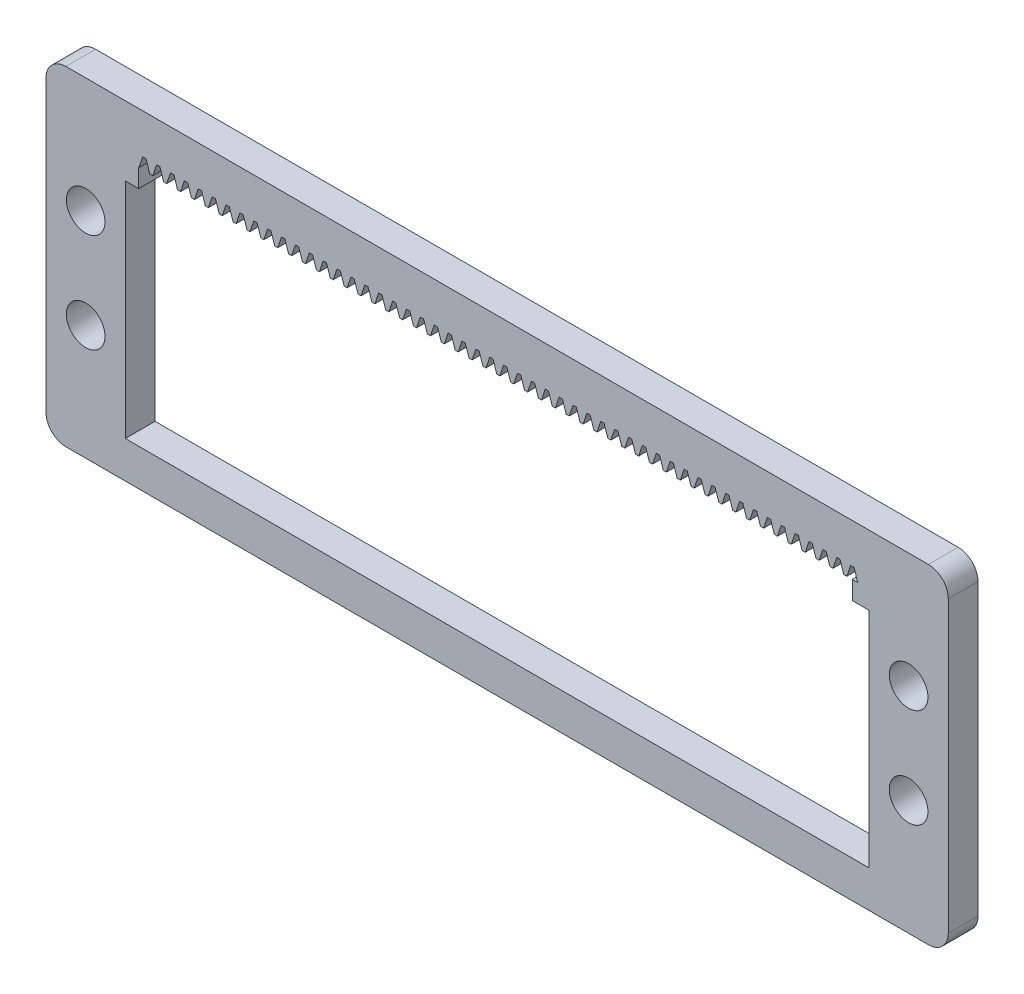
SolidWorks part; units mm, degrees
other "Markup1"
sketch "Sketch6" plane through (0, -30, 3.6) normal (0, 0, 1) x (1, 0, 0)
other "Markup2"
sketch "Sketch7" plane through (0, -30, 3.6) normal (0, 0, 1) x (1, 0, 0)
ref_plane "Front Plane" through (0, 0, 0) normal (0, 0, 1) x (1, 0, 0)
ref_plane "Top Plane" through (0, 0, 0) normal (0, 1, 0) x (1, 0, 0)
ref_plane "Right Plane" through (0, 0, 0) normal (1, 0, 0) x (0, 0, -1)
sketch "Sketch1" plane through (0, 0, 0) normal (0, 0, 1) x (1, 0, 0)
  line L1 (2, 0) -> (89, 0)
  line L2 (0, -2) -> (0, -31.22)
  line L3 (2, -33.22) -> (89, -33.22)
  line L4 (91, -2) -> (91, -31.22)
  arc A0 (89, -33.22) -> (91, -31.22) centre (89, -31.22) ccw
  arc A1 (0, -31.22) -> (2, -33.22) centre (2, -31.22) ccw
  arc A2 (2, 0) -> (0, -2) centre (2, -2) ccw
  arc A3 (89, 0) -> (91, -2) centre (89, -2) cw
  point P7 (91, -33.22)
  point P12 (0, 0)
  point P15 (91, 0)
  dimension "D3" = 2
  dimension "D1" = 33.22
  dimension "D2" = 91
extrude "Boss-Extrude1" add sketch "Sketch1" along normal blind 3
sketch "Sketch2" plane through (0, 0, 3) normal (0, 0, 1) x (1, 0, 0)
  line L0 (2, -33.22) -> (89, -33.22) construction
  line L1 (8, -7) -> (83, -7)
  line L2 (8, -7) -> (8, -29.5)
  line L3 (8, -29.5) -> (83, -29.5)
  line L4 (83, -7) -> (83, -29.5)
  line L5 (0, -2) -> (0, -31.22) construction
  line L7 (91, -31.22) -> (91, -2) construction
  line L8 (8, -18.25) -> (83, -18.25) construction
  line L12 (8, -29.5) -> (83, -29.5) construction
  line L13 (83, -4.3144) -> (83, -29.5) construction
  dimension "D1" = 22.5
  dimension "D2" = 8
  dimension "D3" = 8
  dimension "D4" = 3.72
extrude "Cut-Extrude1" cut sketch "Sketch2" against normal through all
sketch "Sketch3" plane through (0, 0, 3) normal (0, 0, 1) x (1, 0, 0)
  line L0 (83, -7) -> (8, -7) construction
  line L1 (9.35, -7) -> (81.32, -7)
  line L2 (9.35, -7) -> (9.35, -5.15)
  line L3 (9.35, -5.15) -> (81.32, -5.15)
  line L4 (81.32, -7) -> (81.32, -5.15)
  line L5 (83, -29.5) -> (83, -7) construction
  line L6 (8, -7) -> (8, -29.5) construction
  dimension "D1" = 1.85
  dimension "D2" = 1.68
  dimension "D3" = 1.35
extrude "Cut-Extrude2" cut sketch "Sketch3" against normal through all
sketch "Sketch4" plane through (0, 0, 3) normal (0, 0, 1) x (1, 0, 0)
  line L0 (82.345, -5.15) -> (81.865, -5.15) construction
  line L1 (81.32, -5.15) -> (9.35, -5.15) construction
  line L2 (82.345, -5.15) -> (82.725, -4.0118) construction
  line L3 (82.725, -4.0118) -> (81.485, -4.0118) construction
  line L4 (81.485, -4.0118) -> (81.865, -5.15)
  line L5 (81.485, -4.0118) -> (81.155, -4.0118)
  line L6 (81.155, -4.0118) -> (80.775, -5.15)
  line L7 (80.775, -5.15) -> (81.865, -5.15)
  line L10 (81.865, -5.15) -> (82.345, -5.15) construction
  dimension "D1" = 0.48
  dimension "D2" = 1.2
  dimension "D3" = 1.2
  dimension "D4" = 0.33
  dimension "D5" = 1.24
  dimension "D6" = 1.2
extrude "Cut-Extrude4" cut sketch "Sketch4" against normal through all
pattern_linear "LPattern1" count 52 spacing 1.4 along (-1, 0, 0) of "Cut-Extrude4"
sketch "Sketch5" plane through (0, 0, 3) normal (0, 0, 1) x (1, 0, 0)
  line L0 (83, -16.61) -> (91, -16.61) construction
  line L1 (89, 0) -> (2, 0) construction
  line L2 (8, -7) -> (8, -29.5) construction
  line L3 (0, -2) -> (0, -31.22) construction
  line L4 (2, -33.22) -> (89, -33.22) construction
  line L5 (0, -16.61) -> (8, -16.61) construction
  line L7 (87, -11.61) -> (87, -21.61) construction
  line L8 (4, -11.61) -> (4, -21.61) construction
  line L9 (83, -29.5) -> (83, -7) construction
  line L10 (91, -31.22) -> (91, -2) construction
  circle A4 centre (4, -11.61) radius 1.95
  circle A5 centre (4, -21.61) radius 1.95
  circle A6 centre (87, -11.61) radius 1.95
  circle A7 centre (87, -21.61) radius 1.95
  point P8 (87, -16.61)
  point P18 (4, -16.61)
  point P22 (4, -16.61)
  point P31 (87, -16.61)
  dimension "D1" = 3.9
  dimension "D3" = 3.9
  dimension "D4" = 3.9
  dimension "D6" = 3.9
  dimension "D5" = 10
  dimension "D7" = 10
extrude "Cut-Extrude5" cut sketch "Sketch5" against normal blind 10
